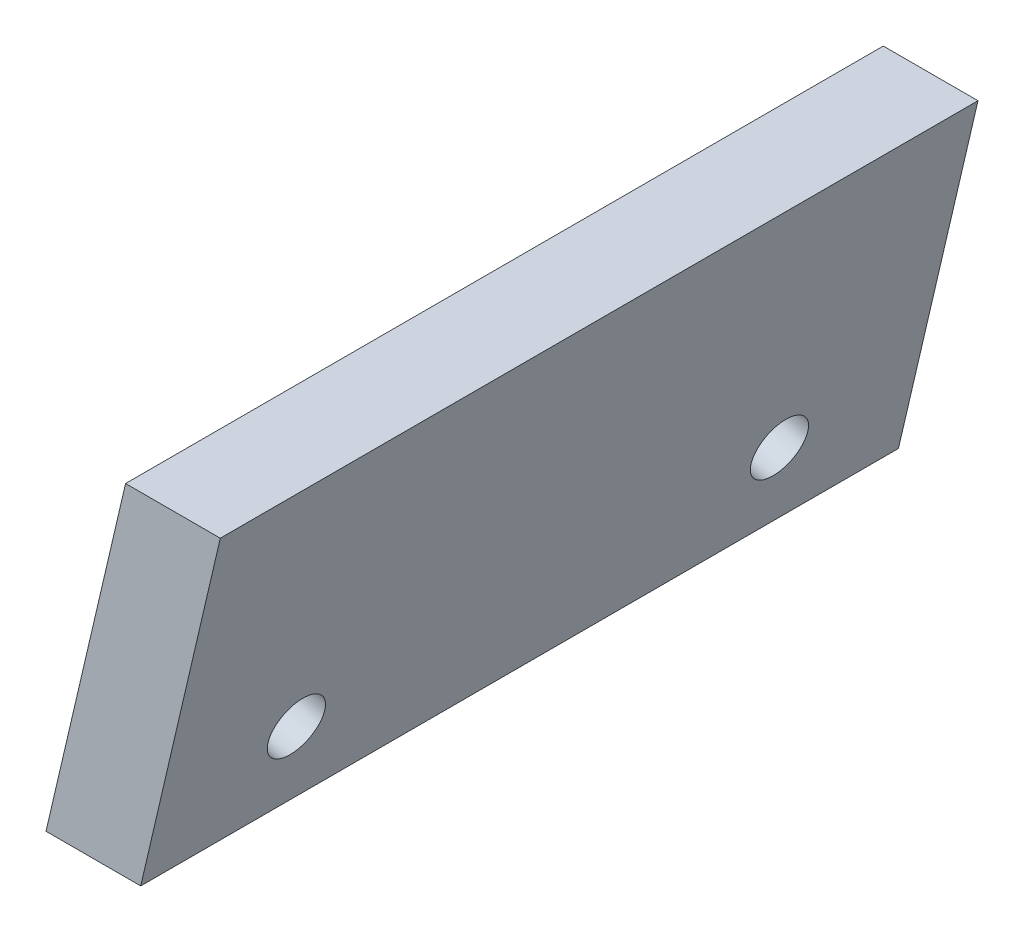
SolidWorks part; units mm, degrees
ref_plane "Front Plane" through (0, 0, 0) normal (0, 0, 1) x (1, 0, 0)
ref_plane "Top Plane" through (0, 0, 0) normal (0, 1, 0) x (1, 0, 0)
ref_plane "Right Plane" through (0, 0, 0) normal (1, 0, 0) x (0, 0, -1)
sketch "Sketch2" plane through (0, 0, 0) normal (0, 0, 1) x (1, 0, 0)
  line L0 (0, 0) -> (2.5, 0)
  line L1 (0, 0) -> (2.1002, 9)
  line L2 (2.5, 0) -> (4.6002, 9)
  line L3 (4.6002, 9) -> (2.1002, 9)
  dimension "D1" = 9
  dimension "D2" = 2.5
extrude "Boss-Extrude2" add sketch "Sketch2" along normal blind 20
sketch "Sketch4" plane through (0, 0, 0) normal (-0.9738, 0.2273, 0) x (0, 0, 1)
  line L0 (0, 9.2418) -> (0, 0) construction
  line L1 (20, 9.2418) -> (20, 0) construction
  line L2 (20, 0) -> (0, 0) construction
  circle A0 centre (3.625, 2.7) radius 0.75
  circle A1 centre (16.375, 2.7) radius 0.75
  dimension "D1" = 3.625
  dimension "D2" = 3.625
  dimension "D3" = 2.7
  dimension "D4" = 2.7
  dimension "D5" = 1.5
  dimension "D6" = 1.5
extrude "Cut-Extrude1" cut sketch "Sketch4" against normal through all
